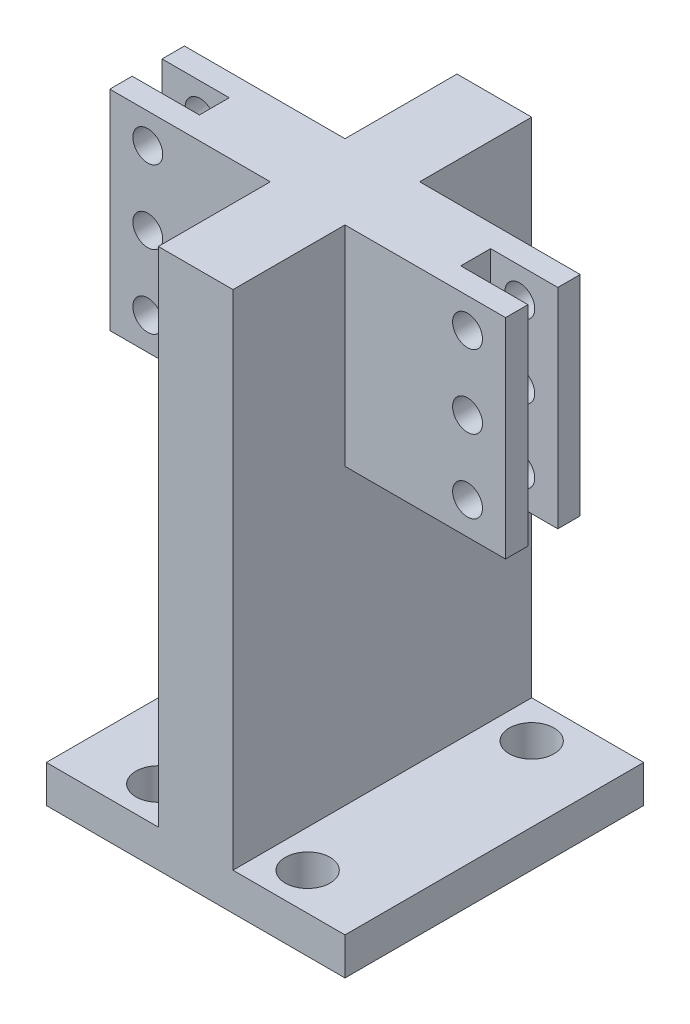
SolidWorks part; units mm, degrees
ref_plane "Front" through (0, 0, 0) normal (0, 0, 1) x (1, 0, 0)
ref_plane "Top" through (0, 0, 0) normal (0, 1, 0) x (1, 0, 0)
ref_plane "Right" through (0, 0, 0) normal (1, 0, 0) x (0, 0, -1)
sketch "草图1" plane through (0, 0, 0) normal (0, 1, 0) x (1, 0, 0)
  line L0 (0, -20) -> (0, 20) construction
  line L1 (-20, 20) -> (20, 20) construction
  line L2 (20, 20) -> (20, -20) construction
  line L3 (20, 0) -> (0, 0) construction
  line L4 (10, -15) -> (10, 15) construction
  line L5 (-10, -15) -> (-10, 15) construction
  line L6 (-20, 20) -> (-20, -20) construction
  line L7 (-20, -20) -> (20, -20) construction
  line L8 (-20, 20) -> (20, 20)
  line L9 (20, 20) -> (20, -20)
  line L10 (20, -20) -> (-20, -20)
  line L11 (-20, -20) -> (-20, 20)
  circle A0 centre (-10, -15) radius 3
  circle A1 centre (10, -15) radius 3
  circle A2 centre (10, 15) radius 3
  circle A3 centre (-10, 15) radius 3
  point P13 (10, 0)
  point P14 (-10, 0)
  point P16 (-20, 0)
extrude "凸台-拉伸1" add sketch "草图1" along normal blind 5
sketch "草图2" plane through (0, 5, 0) normal (0, 1, 0) x (1, 0, 0)
  line L0 (0, 0) -> (-20, 0) construction
  line L1 (-20, 20) -> (-20, -20) construction
  line L2 (-20, 0) -> (-10, 0) construction
  line L3 (-10, 0) -> (0, 0) construction
  line L4 (0, 0) -> (-5, 0) construction
  line L5 (-5, 0) -> (-5, 20) construction
  line L6 (20, 20) -> (-20, 20) construction
  line L7 (-5, 20) -> (-5, -20) construction
  line L8 (-20, -20) -> (20, -20) construction
  line L9 (0, 0) -> (20, 0) construction
  line L10 (20, -20) -> (20, 20) construction
  line L11 (20, 0) -> (10, 0) construction
  line L12 (10, 0) -> (0, 0) construction
  line L13 (0, 0) -> (5, 0) construction
  line L14 (5, 0) -> (5, 20) construction
  line L15 (5, 20) -> (5, -20) construction
  line L16 (-5, 20) -> (5, 20)
  line L17 (5, 20) -> (5, -20)
  line L18 (5, -20) -> (-5, -20)
  line L19 (-5, -20) -> (-5, 20)
extrude "凸台-拉伸2" add sketch "草图2" along normal blind 67.34
sketch "草图3" plane through (-5, 0, 0) normal (-1, 0, 0) x (0, 0, 1)
  line L0 (0, 72.34) -> (0, 44.34) construction
  line L1 (-20, 72.34) -> (20, 72.34) construction
  line L2 (0, 44.34) -> (20, 44.34) construction
  line L3 (20, 72.34) -> (20, 5) construction
  line L4 (20, 44.34) -> (-20, 44.34) construction
  line L5 (-20, 72.34) -> (-20, 5) construction
  line L10 (-20, 44.34) -> (0, 44.34) construction
  line L11 (0, 44.34) -> (-10, 44.34) construction
  line L12 (-10, 44.34) -> (-10, 72.34) construction
  line L13 (-10, 72.34) -> (0, 72.34) construction
  line L14 (0, 72.34) -> (20, 72.34) construction
  line L15 (20, 72.34) -> (10, 72.34) construction
  line L16 (10, 72.34) -> (10, 44.34) construction
  line L17 (10, 44.34) -> (0, 44.34) construction
  line L18 (0, 44.34) -> (5, 44.34) construction
  line L19 (5, 44.34) -> (5, 72.34) construction
  line L20 (5, 72.34) -> (0, 72.34) construction
  line L21 (0, 72.34) -> (-10, 72.34) construction
  line L22 (-10, 72.34) -> (-5, 72.34) construction
  line L23 (-5, 72.34) -> (-5, 44.34) construction
  line L24 (-5, 44.34) -> (0, 44.34) construction
  line L25 (-5, 72.34) -> (-5, 44.34)
  line L26 (-5, 44.34) -> (5, 44.34)
  line L27 (5, 44.34) -> (5, 72.34)
  line L28 (5, 72.34) -> (-5, 72.34)
extrude "凸台-拉伸3" add sketch "草图3" along normal blind 24.5
sketch "草图5" plane through (0, 0, 0) normal (0, 0, 1) x (1, 0, 0)
  line L0 (-29.5, 72.34) -> (-17.5, 72.34) construction
  line L1 (-29.5, 72.34) -> (-5, 72.34) construction
  line L2 (-21.41, 58.49) -> (-21.41, 48.67) construction
  line L4 (-21.41, 72.34) -> (-21.41, 68.31) construction
  line L5 (-29.5, 72.34) -> (-17.5, 72.34) construction
  line L6 (-17.5, 72.34) -> (-17.5, 44.34) construction
  line L7 (-17.5, 44.34) -> (-29.5, 44.34) construction
  line L8 (-21.41, 68.31) -> (-17.5, 68.31) construction
  line L9 (-17.5, 68.31) -> (-17.5, 58.49) construction
  line L10 (-17.5, 58.49) -> (-21.41, 58.49) construction
  circle A3 centre (-21.41, 68.31) radius 2
  circle A4 centre (-21.41, 58.49) radius 2
  circle A5 centre (-21.41, 48.67) radius 2
extrude "切除-拉伸1" cut sketch "草图5" against normal mid plane 24.5
sketch "草图6" plane through (0, 0, 0) normal (0, 0, 1) x (1, 0, 0)
  line L0 (-29.5, 72.34) -> (-17.5, 72.34) construction
  line L1 (-29.5, 72.34) -> (-5, 72.34) construction
  line L2 (-17.5, 72.34) -> (-17.5, 44.34) construction
  line L3 (-29.5, 44.34) -> (-5, 44.34) construction
  line L4 (-29.5, 72.34) -> (-17.5, 72.34)
  line L5 (-17.5, 72.34) -> (-17.5, 44.34)
  line L6 (-17.5, 44.34) -> (-29.5, 44.34)
  line L7 (-29.5, 44.34) -> (-29.5, 72.34)
extrude "切除-拉伸2" cut sketch "草图6" against normal mid plane 4
mirror "镜向1" about plane through (0, 0, 0) normal (1, 0, 0) of "切除-拉伸1", "切除-拉伸2", "凸台-拉伸3"
sketch "草图7" plane through (0, 0, 0) normal (0, 0, 1) x (1, 0, 0)
  line L0 (-29.5, 72.34) -> (-26.5, 72.34) construction
  line L1 (-29.5, 72.34) -> (-5, 72.34) construction
  line L2 (-26.5, 72.34) -> (-26.5, 44.34) construction
  line L3 (-29.5, 44.34) -> (-5, 44.34) construction
  line L4 (-26.5, 44.34) -> (-29.5, 44.34) construction
  line L5 (-29.5, 44.34) -> (-29.5, 72.34) construction
  line L6 (-29.5, 72.34) -> (-26.5, 72.34)
  line L7 (-26.5, 72.34) -> (-26.5, 44.34)
  line L8 (-26.5, 44.34) -> (-29.5, 44.34)
  line L9 (-29.5, 44.34) -> (-29.5, 72.34)
extrude "切除-拉伸3" cut sketch "草图7" against normal mid plane 50
mirror "镜向2" about plane through (0, 0, 0) normal (1, 0, 0) of "切除-拉伸3"
